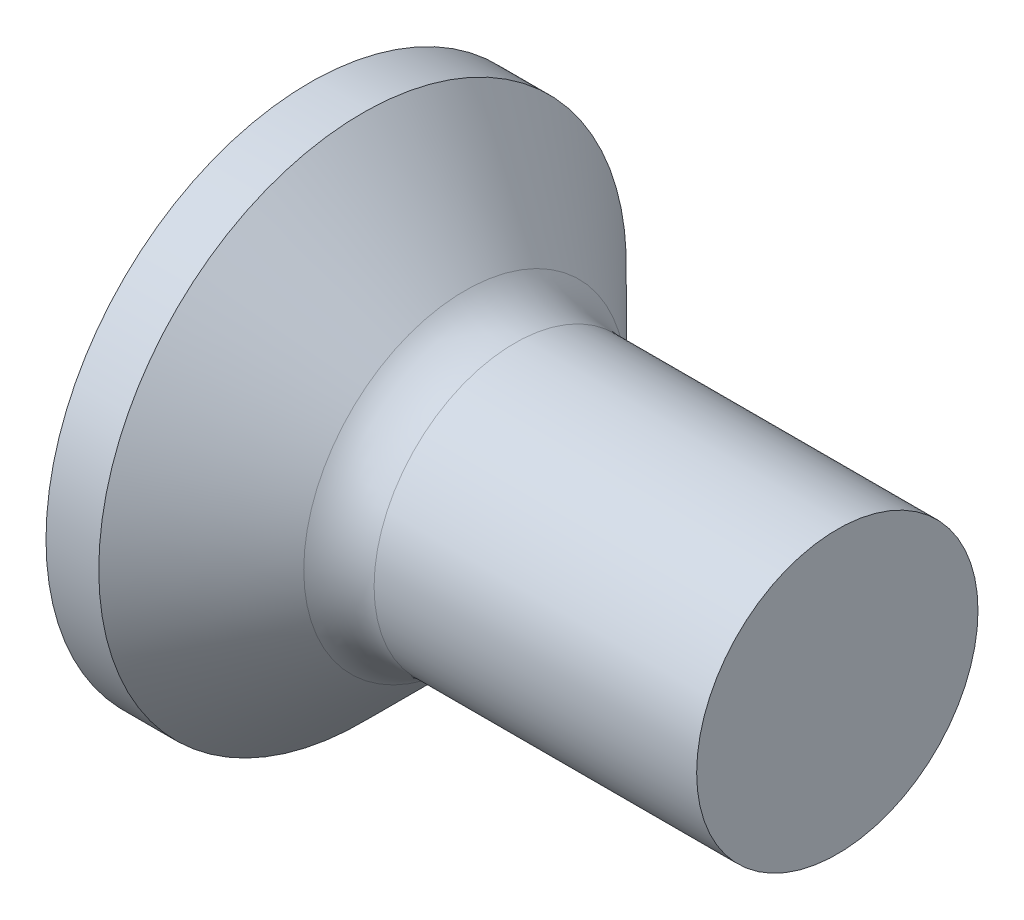
SolidWorks part; units mm, degrees
ref_plane "Plane1" through (0, 0, 0) normal (0, 0, 1) x (1, 0, 0)
ref_plane "Plane2" through (0, 0, 0) normal (0, 1, 0) x (1, 0, 0)
ref_plane "Plane3" through (0, 0, 0) normal (1, 0, 0) x (0, 0, -1)
sketch "BodySke" plane through (0, 0, 0) normal (0, 0, 1) x (1, 0, 0)
  line L0 (0, 0) -> (3.4, 0)
  line L1 (3.4, 0) -> (3.4, 0.8)
  line L2 (3.4, 0.8) -> (1.4, 0.8)
  line L3 (0.7, -1.5) -> (1.4, -0.8) construction
  line L4 (-15.875, 0) -> (82.55, 0) construction
  line L5 (0.7, 1.5) -> (1.4, 0.8)
  line L6 (1.75, 3.975) -> (1.75, -11.9) construction
  line L7 (0.4, 2.7793) -> (0.4, -13.0957) construction
  line L8 (0.7, 1.5) -> (0.4, 1.5)
  arc A0 (0, 0) -> (0.4, 1.5) centre (3.0125, 0) cw
  dimension "Length" = 3
  dimension "Diameter" = 1.6
  dimension "Head_dia" = 3
  dimension "Head_ang" = 90
  dimension "Advance" = 0.35
  dimension "Thread_nom" = 3
  dimension "Oval_ht" = 0.4
  dimension "Side_ht" = 1
revolve "Base-Revolve" add sketch "BodySke" angle 360 about L4
cosmetic thread "ThreadCosmetic" [suppressed] parameters "Thread_length"=1.65, "Thread_minor"=1.202
fillet "Fillet1" radius 0.4 1 edges at (1.4, 0, 0.8)
sketch "Sketch3" plane through (0, 0, 0) normal (1, 0, 0) x (0, 0, -1)
  line L0 (0.24, -0.95) -> (-0.24, -0.95)
  line L1 (0.24, -0.95) -> (0.24, 0.95)
  line L2 (-0.24, 0.95) -> (0.24, 0.95)
  line L3 (-0.24, 0.95) -> (-0.24, -0.95)
  dimension "D1" = 0.24
  dimension "Cross_width" = 0.48
  dimension "D2" = 0.95
  dimension "Cross_dia" = 1.9
ref_plane "Plane4" through (1.2, 0, 0) normal (1, 0, 0) x (0, 0, -1)
sketch "Sketch4" plane through (1.2, 0, 0) normal (1, 0, 0) x (0, 0, -1)
  line L0 (0.24, -0.3517) -> (-0.24, -0.3517)
  line L1 (0.24, -0.3517) -> (0.24, 0.3517)
  line L2 (-0.24, 0.3517) -> (0.24, 0.3517)
  line L3 (-0.24, 0.3517) -> (-0.24, -0.3517)
  dimension "D1" = 0.48
  dimension "D2" = 0.7034
  dimension "D3" = 0.24
  dimension "D4" = 0.3517
loft "Recess" cut profiles "Sketch3", "Sketch4"
pattern_circular "RecPat" count 2 every 90 about axis through (0, 0, 0) along (1, 0, 0) of "Recess"
sketch "RecCorSke" plane through (0, 0, 0) normal (0, 0, 1) x (1, 0, 0)
  line L0 (-3.175, 0) -> (15.875, 0) construction
  line L2 (0, 0) -> (0, 0.4394)
  line L3 (0, 0.4394) -> (1.2, 0.3555)
  line L4 (1.2, 0.3555) -> (1.3155, 0)
  line L5 (1.3155, 0) -> (0, 0)
  dimension "Diameter" = 0.711
  dimension "Depth" = 1.2
  dimension "Draft_angle" = 4
  dimension "Bottom_angle" = 18
revolve "RecessCore" cut sketch "RecCorSke" angle 360 about L0
sketch "ThdSchSke" plane through (0, 0, 0) normal (0, 0, 1) x (1, 0, 0)
  line L0 (1.75, -0.601) -> (1.6107, -0.8)
  line L1 (1.75, -0.601) -> (1.8893, -0.8)
  line L2 (1.8893, -0.8) -> (1.8893, -1)
  line L3 (-3.175, 0) -> (5.1513, 0) construction
  line L5 (1.8893, -1) -> (1.6107, -1)
  line L6 (1.6107, -1) -> (1.6107, -0.8)
  dimension "Thread_minor" = 1.202
  dimension "Diameter" = 1.6
  dimension "Start" = 1.75
  dimension "SideAngle" = 55
  dimension "VeeAngle" = 70
  dimension "Overcut" = 2
revolve "ThreadSchematic" [suppressed] cut sketch "ThdSchSke" angle 360 about L3
pattern_linear "ThdSchPat" [suppressed]
equation "\"D1@Sketch3\" = \"Cross_width@Sketch3\" / 2"
equation "\"D2@Sketch3\" = \"Cross_dia@Sketch3\" / 2"
equation "\"Depth@RecCorSke\" = \"Cross_depth@Plane4\""
equation "\"D1@Sketch4\" = \"Cross_width@Sketch3\""
equation "\"D2@Sketch4\" = \"Cross_dia@Sketch3\" - 2.0 * \"Cross_depth@Plane4\" * tan(26.5  * 0.017453292)"
equation "\"D3@Sketch4\" = \"D1@Sketch4\" / 2"
equation "\"D4@Sketch4\" = \"D2@Sketch4\" / 2"
equation "\"Thread_length@ThreadCosmetic\" = ((sgn( (\"Length@BodySke\" - \"Advance@BodySke\" - \"Side_ht@BodySke\" ) - \"Thread_nom@BodySke\" )-1)*( (\"Length@BodySke\" - \"Advance@BodySke\" - \"Side_ht@BodySke\" ) - \"Thread_nom@BodySke\" ))/-2+ \"Thread_nom@BodySke\""
equation "\"Thread_minor@ThdSchSke\" = \"Thread_minor@ThreadCosmetic\""
equation "\"Diameter@ThdSchSke\" = \"Diameter@BodySke\""
equation "\"Overcut@ThdSchSke\" = \"Diameter@BodySke\" * 1.25"
equation "\"Start@ThdSchSke\" = \"Oval_ht@BodySke\" + \"Length@BodySke\" - \"Thread_length@ThreadCosmetic\"  '---Countersunk---"
equation "\"Num_threads@ThdSchPat\" = int( \"Thread_length@ThreadCosmetic\" / \"Advance@BodySke\" + 0.999 )  + 1"
equation "\"Advance@ThdSchPat\" = \"Thread_length@ThreadCosmetic\" /  (\"Num_threads@ThdSchPat\" - 1) 'relax it"
